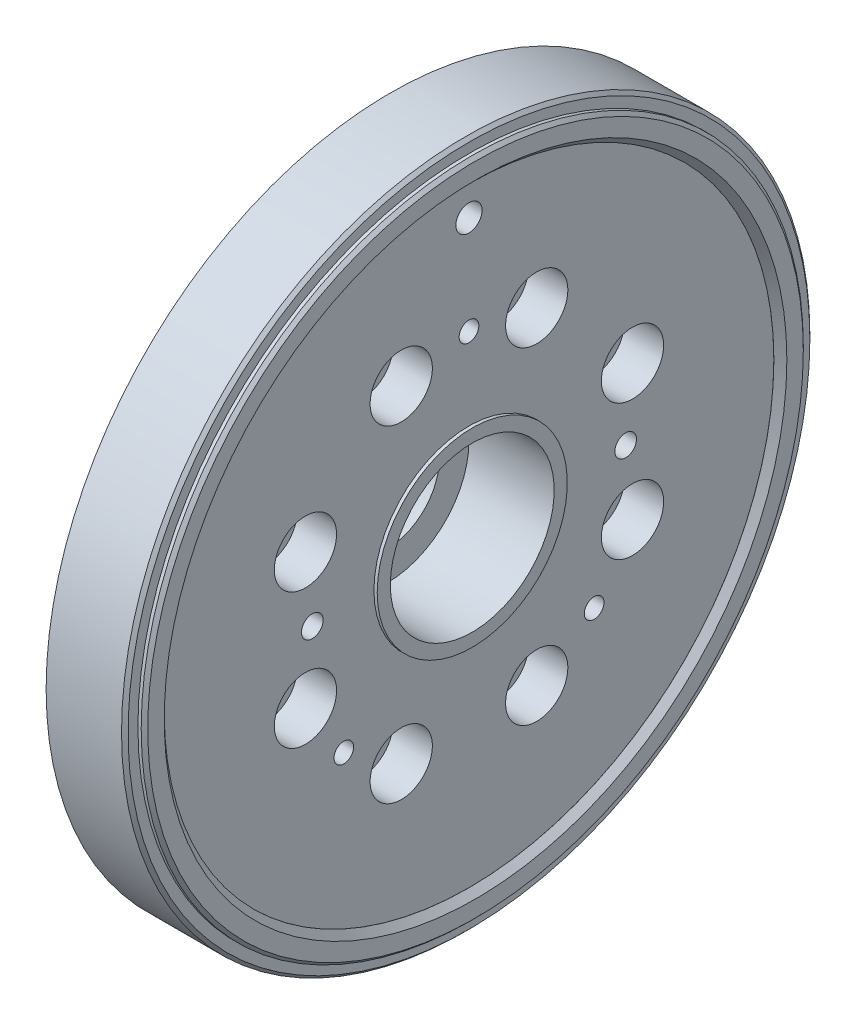
SolidWorks part; units mm, degrees
ref_plane "Ebene vorne" through (0, 0, 0) normal (0, 0, 1) x (1, 0, 0)
ref_plane "Ebene oben" through (0, 0, 0) normal (0, 1, 0) x (1, 0, 0)
ref_plane "Ebene rechts" through (0, 0, 0) normal (1, 0, 0) x (0, 0, -1)
sketch "Skizze1" plane through (0, 0, 0) normal (0, 0, 1) x (1, 0, 0)
  line L0 (-20.8065, 0) -> (104.7581, 0) construction
  line L1 (0, 0) -> (0, -10)
  line L2 (13, -52.5) -> (25, -52.5)
  line L3 (0, -10) -> (11, -10)
  line L4 (11, -10) -> (11, -15)
  line L9 (11, -15) -> (13, -15)
  line L10 (13, -15) -> (13, -31)
  line L11 (0, 0) -> (25, 0)
  line L12 (25, -12.5) -> (25, 0)
  line L13 (13, -31) -> (16, -31)
  line L14 (16, -31) -> (16, -37)
  line L15 (16, -37) -> (13, -37)
  line L16 (13, -37) -> (13, -41)
  line L17 (13, -41) -> (16, -41)
  line L18 (16, -41) -> (16, -49)
  line L19 (13, -52.5) -> (16, -49)
  line L20 (25, -12.5) -> (25.5, -12.5)
  line L21 (25.5, -12.5) -> (25.5, -14.5)
  line L22 (25.5, -14.5) -> (25, -14.5)
  line L23 (25, -14.5) -> (25, -46.5)
  line L24 (25, -50.5) -> (26, -50.5)
  line L25 (26, -50.5) -> (26, -46.5)
  line L26 (26, -46.5) -> (25, -46.5)
  line L27 (25, -50.5) -> (25, -52.5)
  dimension "D1" = 52.5
  dimension "D9" = 10
  dimension "D10" = 5
  dimension "D11" = 2
  dimension "D12" = 12.5
  dimension "D13" = 11
  dimension "D14" = 3
  dimension "D15" = 62
  dimension "D16" = 6
  dimension "D17" = 4
  dimension "D18" = 8
  dimension "D19" = 3
  dimension "D20" = 0
  dimension "D21" = 0.5
  dimension "D22" = 2
  dimension "D23" = 93
  dimension "D24" = 4
  dimension "D25" = 25
  dimension "D26" = 1
  dimension "D27" = 2
revolve "Rotation1" add sketch "Skizze1" angle 360 about L0
sketch "Skizze22" plane through (25, 0, 0) normal (1, 0, 0) x (0, 0, -1)
  circle A0 centre (0, 0) radius 12.5
  dimension "D1" = 25
extrude "Schnitt-Linear austragen16" cut sketch "Skizze22" against normal blind 12.5
sketch "Skizze23" plane through (25, 0, 0) normal (1, 0, 0) x (0, 0, -1)
  line L0 (0, 0) -> (0, 27) construction
  line L1 (0, 0) -> (-19.0919, -19.0919) construction
  line L2 (0, 0) -> (19.0919, -19.0919) construction
  circle A0 centre (0, 0) radius 27 construction
  circle A1 centre (0, 27) radius 1.5
  circle A2 centre (-19.0919, -19.0919) radius 1.5
  circle A3 centre (19.0919, -19.0919) radius 1.5
  dimension "D1" = 54
  dimension "D4" = 3
  dimension "D5" = 3
  dimension "D6" = 3
  dimension "D2" = 45
  dimension "D3" = 45
extrude "Schnitt-Linear austragen17" cut sketch "Skizze23" against normal up to next
sketch "Skizze24" plane through (25, 0, 0) normal (1, 0, 0) x (0, 0, -1)
  line L0 (0, 1.5042) -> (0, -3.61) construction
  line L1 (0, 0) -> (10.3325, 24.9447) construction
  circle A0 centre (0, 0) radius 27 construction
  circle A1 centre (10.3325, 24.9447) radius 2.75
  dimension "D2" = 5.5
  dimension "D3" = 54
  dimension "D1" = 22.5
extrude "Schnitt-Linear austragen18" cut sketch "Skizze24" against normal through all
pattern_circular "Kreismuster4" count 8 over 360 about axis through (0, 0, 0) along (1, 0, 0) of "Schnitt-Linear austragen18"
sketch "Skizze25" plane through (25, 0, 0) normal (1, 0, 0) x (0, 0, -1)
  circle A0 centre (10.3325, 24.9447) radius 4.75
  dimension "D1" = 9.5
extrude "Schnitt-Linear austragen19" cut sketch "Skizze25" against normal blind 6
pattern_circular "Kreismuster5" count 8 over 360 about axis through (0, 0, 0) along (1, 0, 0) of "Schnitt-Linear austragen19"
sketch "Skizze26" plane through (25, 0, 0) normal (1, 0, 0) x (0, 0, -1)
  circle A0 centre (0, 42) radius 2
  dimension "D1" = 4
  dimension "D2" = 42
extrude "Schnitt-Linear austragen20" cut sketch "Skizze26" against normal blind 6 and the other way through all contours A0
sketch "Skizze27" plane through (12.5, 0, 0) normal (1, 0, 0) x (0, 0, -1)
  circle A0 centre (0, 0) radius 8
  dimension "D1" = 16
extrude "Schnitt-Linear austragen21" cut sketch "Skizze27" against normal through all contours A0
fillet "Verrundung8" radius 0.2 3 edges at (13, 0, 31) (11, 0, 15) (0, 0, 10)
fillet "Verrundung9" radius 0.2 2 edges at (13, 0, 37) (13, 0, 41)
chamfer "Fase6" distance 0.99 angle 45 1 edges at (26, 0, 46.5)
hole_wizard "M4 Gewindebohrung1" positions "Skizze28" profile "Skizze29" tap size "M4" standard "DIN"
sketch "Skizze28" plane through (25, 0, 0) normal (1, 0, 0) x (0, 0, -1)
  circle A0 centre (0, 0) radius 23.9 construction
  point P0 (-23.9, 0)
  point P2 (23.9, 0)
  dimension "D1" = 47.8
sketch "Skizze29" plane through (25, 0, 23.9) normal (0, 1, 0) x (0, 0, -1)
  line L0 (0, 0) -> (0, 10.9914)
  line L1 (0, 10.9914) -> (1.65, 10)
  line L2 (1.65, 10) -> (1.65, 0)
  line L5 (1.65, 0) -> (0, 0)
  line L10 (0, 10.9914) -> (-1.65, 10) construction
  line L11 (0, -6.35) -> (0, 107.95) construction
  dimension "Bohrerdurchmesser" = 3.3
  dimension "Bohrungstiefe" = 10
  dimension "Spitzenwinkel" = 118
cosmetic thread "Bohrungsgewinde1" parameters "D1"=7, "D2"=4
cosmetic thread "Bohrungsgewinde2" parameters "D1"=7, "D2"=4
chamfer "Fase7" distance 0.5 angle 45 2 edges at (26, 0, 50.5) (25, 0, 52.5)
chamfer "Fase8" distance 0.25 angle 45 1 edges at (0, 0, -8)
sketch "Skizze30" plane through (25, 0, 0) normal (1, 0, 0) x (0, 0, -1)
  line L0 (-0.25, 52.4994) -> (0.25, 52.4994)
  line L1 (0, 0) -> (0, 64.3127) construction
  line L2 (-0.25, 52.4994) -> (-0.25, 52.8994)
  line L3 (-0.15, 52.9994) -> (0.15, 52.9994)
  line L4 (0.25, 52.8994) -> (0.25, 52.4994)
  circle A0 centre (0, 0) radius 52.5 construction
  arc A1 (-0.15, 52.9994) -> (-0.25, 52.8994) centre (-0.15, 52.8994) ccw
  arc A2 (0.15, 52.9994) -> (0.25, 52.8994) centre (0.15, 52.8994) cw
  point P8 (-0.25, 52.9994)
  point P11 (-0.25, 52.9994)
  point P12 (-0.25, 52.9925)
  point P14 (-0.25, 52.9994)
  dimension "D5" = 0.1
  dimension "D1" = 0.5
  dimension "D2" = 90
  dimension "D3" = 0.25
  dimension "D4" = 0.5
